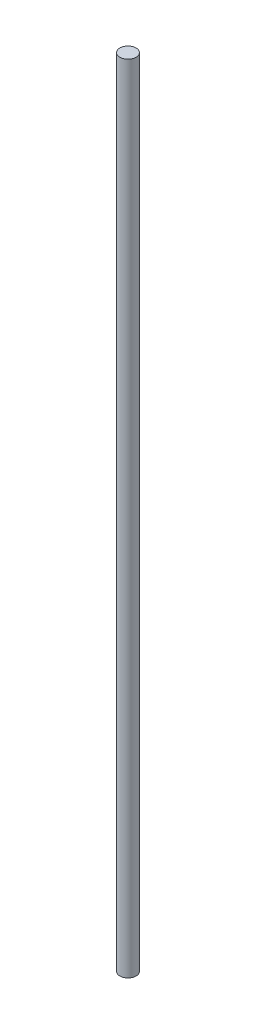
SolidWorks part; units mm, degrees
ref_plane "Front Plane" through (0, 0, 0) normal (0, 0, 1) x (1, 0, 0)
ref_plane "Top Plane" through (0, 0, 0) normal (0, 1, 0) x (1, 0, 0)
ref_plane "Right Plane" through (0, 0, 0) normal (1, 0, 0) x (0, 0, -1)
sketch "Sketch1" plane through (0, 0, 0) normal (0, 1, 0) x (1, 0, 0)
  circle A0 centre (0, 0) radius 4.0005
  dimension "D1" = 8.001
extrude "Boss-Extrude1" add sketch "Sketch1" along normal blind 393.7
